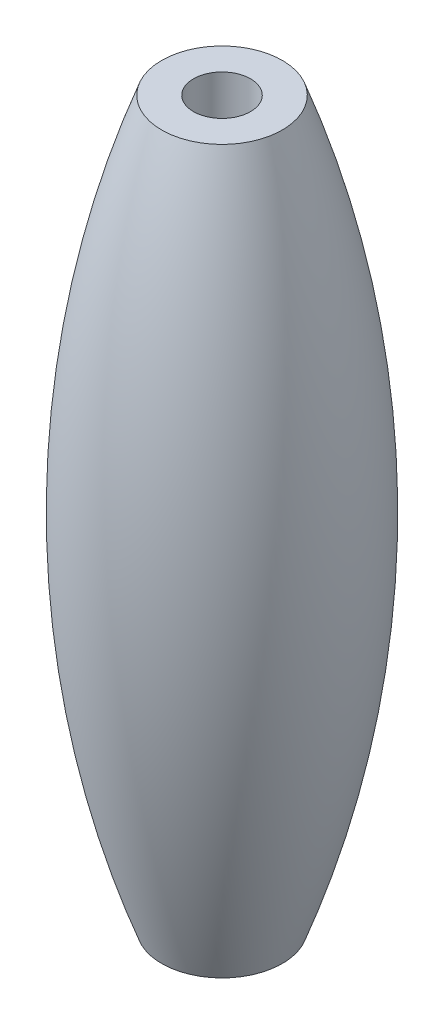
SolidWorks part; units mm, degrees
ref_plane "Front Plane" through (0, 0, 0) normal (0, 0, 1) x (1, 0, 0)
ref_plane "Top Plane" through (0, 0, 0) normal (0, 1, 0) x (1, 0, 0)
ref_plane "Right Plane" through (0, 0, 0) normal (1, 0, 0) x (0, 0, -1)
sketch "Sketch1" plane through (0, 0, 0) normal (0, 0, 1) x (1, 0, 0)
  line L0 (0, 17.8713) -> (3.175, 17.8713)
  line L1 (0, 17.8713) -> (0, -20.1287)
  line L2 (0, -20.1287) -> (3.175, -20.1287)
  arc A0 (3.175, 17.8713) -> (3.175, -20.1287) centre (-48.781, -1.1287) cw
  point P8 (4.0105, 0)
revolve "Revolve1" add sketch "Sketch1" angle 360 about L1
hole_wizard "Ø3.0mm Dowel Hole1" positions "3DSketch1" profile "Sketch2" hole size "Ø3.0" standard "ANSI Metric" end condition through all
sketch3d "3DSketch1"
  line L0 (0, -9.5814, 0) -> (0, 15.7766, 0) construction
  point P0 (0, 17.8713, 0)
sketch "Sketch2" plane through (0, 17.8713, 0) normal (1, 0, 0) x (0, 0, 1)
  line L0 (0, 0) -> (0, 38)
  line L1 (0, 38) -> (1.5, 38)
  line L2 (1.5, 38) -> (1.5, 0)
  line L5 (1.5, 0) -> (0, 0)
  line L11 (0, -6.35) -> (0, 107.95) construction
  dimension "Thru Hole Dia." = 3
  dimension "Thru Hole Depth" = 38
